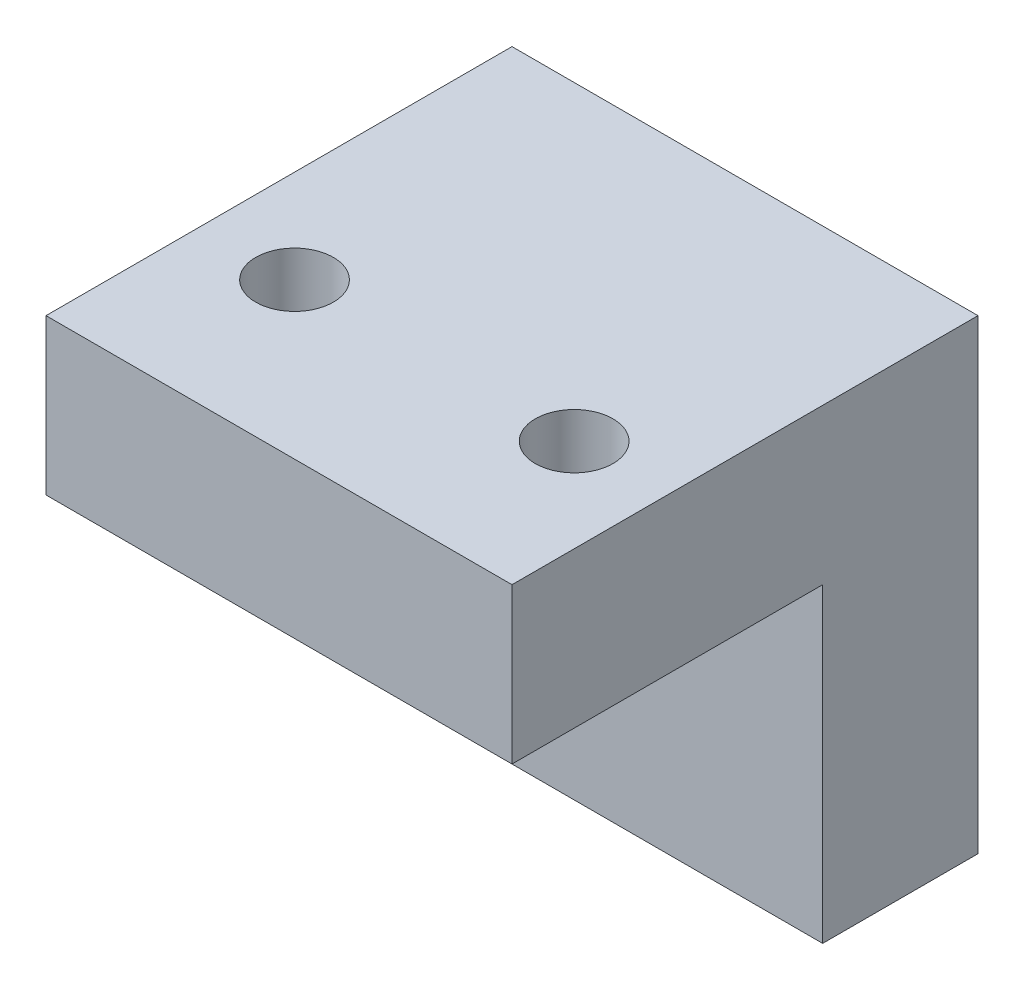
SolidWorks part; units mm, degrees
material "1060 合金"
ref_plane "前视基准面" through (0, 0, 0) normal (0, 0, 1) x (1, 0, 0)
ref_plane "上视基准面" through (0, 0, 0) normal (0, 1, 0) x (1, 0, 0)
ref_plane "右视基准面" through (0, 0, 0) normal (1, 0, 0) x (0, 0, -1)
sketch "草图1" plane through (0, 0, 0) normal (0, 1, 0) x (1, 0, 0)
  line L1 (0, 0) -> (15, 0)
  line L2 (0, 0) -> (0, 5)
  line L3 (0, 5) -> (15, 5)
  line L4 (15, 0) -> (15, 5)
  dimension "D1" = 5
  dimension "D2" = 15
extrude "凸台-拉伸1" add sketch "草图1" along normal blind 10
sketch "草图2" plane through (0, 10, 0) normal (0, 1, 0) x (1, 0, 0)
  line L0 (15, 0) -> (15, 5) construction
  line L1 (0, 5) -> (15, 5)
  line L2 (0, 5) -> (0, -10)
  line L3 (0, -10) -> (15, -10)
  line L4 (15, 5) -> (15, -10)
  dimension "D1" = 15
extrude "凸台-拉伸2" add sketch "草图2" along normal blind 5
sketch "草图3" plane through (0, 0, 0) normal (0, 0, 1) x (1, 0, 0)
  line L0 (7.5, 0) -> (7.5, 10) construction
  line L1 (0, 0) -> (15, 0) construction
  line L2 (0, 10) -> (15, 10) construction
  circle A3 centre (7.5, 5) radius 1.25
  dimension "D1" = 5
  dimension "D2" = 2.5
extrude "切除-拉伸1" cut sketch "草图3" against normal through all
sketch "草图4" plane through (0, 15, 0) normal (0, 1, 0) x (1, 0, 0)
  line L0 (0, -10) -> (15, -10) construction
  line L1 (0, 5) -> (0, -10) construction
  circle A2 centre (3, -5) radius 1.25
  circle A3 centre (12, -5) radius 1.25
  dimension "D1" = 9
  dimension "D2" = 5
  dimension "D4" = 2.5
  dimension "D3" = 3
extrude "切除-拉伸2" cut sketch "草图4" against normal blind 5
move or copy body "实体-移动/复制1" [suppressed] bodies to move or copy 109
